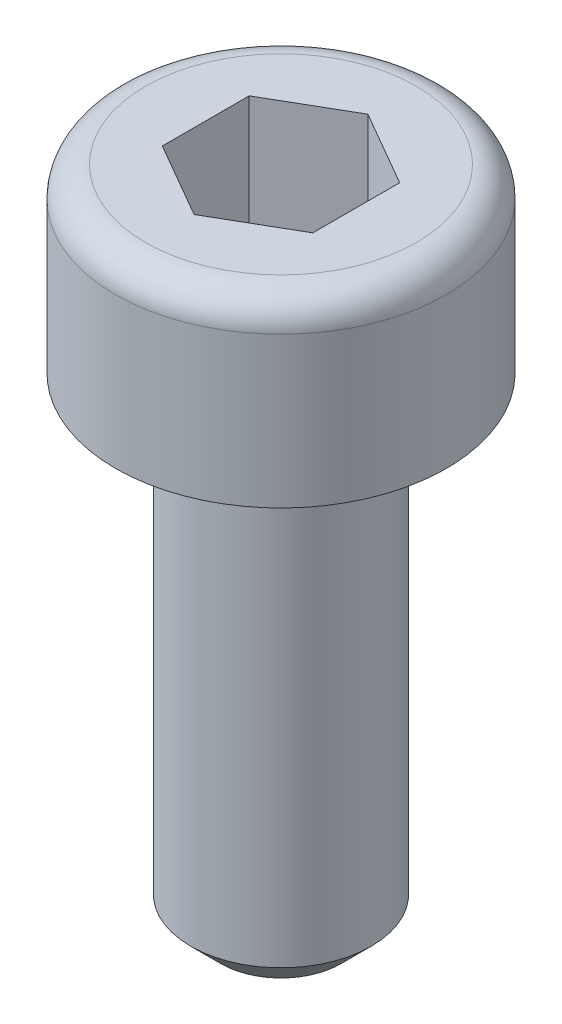
SolidWorks part; units mm, degrees
material "acero"
ref_plane "Alzado" through (0, 0, 0) normal (0, 0, 1) x (1, 0, 0)
ref_plane "Planta" through (0, 0, 0) normal (0, 1, 0) x (1, 0, 0)
ref_plane "Vista lateral" through (0, 0, 0) normal (1, 0, 0) x (0, 0, -1)
sketch "Croquis1" plane through (0, 0, 0) normal (0, 0, 1) x (1, 0, 0)
  line L0 (0, 0) -> (0, -60.9498) construction
  line L1 (0, 0) -> (2.75, 0)
  line L2 (2.75, 0) -> (2.75, -3)
  line L3 (2.75, -3) -> (1.5, -3)
  line L4 (1.5, -3) -> (1.5, -11)
  line L5 (1.5, -11) -> (0, -11)
  line L6 (0, -11) -> (0, 0)
  dimension "D1" = 8
  dimension "D2" = 3
  dimension "D3" = 5.5
  dimension "D4" = 3
revolve "Revolución1" add sketch "Croquis1" angle 360 about L0
sketch "Croquis2" plane through (0, 0, 0) normal (0, 1, 0) x (1, 0, 0)
  line L1 (1.25, 0.7217) -> (0, 1.4434)
  line L2 (0, 1.4434) -> (-1.25, 0.7217)
  line L3 (-1.25, 0.7217) -> (-1.25, -0.7217)
  line L4 (-1.25, -0.7217) -> (0, -1.4434)
  line L5 (0, -1.4434) -> (1.25, -0.7217)
  line L6 (1.25, -0.7217) -> (1.25, 0.7217)
  circle A0 centre (0, 0) radius 1.25 construction
  dimension "D1" = 2.5
extrude "Cortar-Extruir1" cut sketch "Croquis2" against normal blind 2
chamfer "Chaflán1" distance 0.5 angle 45 1 edges at (0, -11, 1.5)
fillet "Redondeo1" radius 0.5 1 edges at (0, 0, 2.75)
